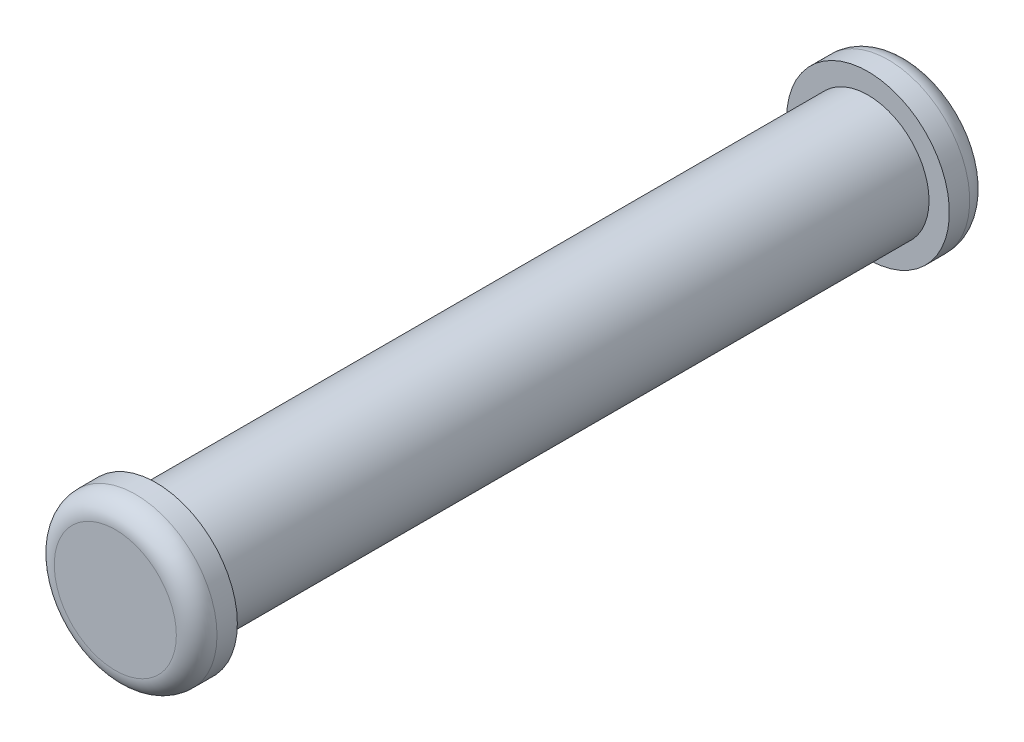
SolidWorks part; units mm, degrees
ref_plane "Front Plane" through (0, 0, 0) normal (0, 0, 1) x (1, 0, 0)
ref_plane "Top Plane" through (0, 0, 0) normal (0, 1, 0) x (1, 0, 0)
ref_plane "Right Plane" through (0, 0, 0) normal (1, 0, 0) x (0, 0, -1)
sketch "Sketch1" plane through (0, 0, 0) normal (0, 0, 1) x (1, 0, 0)
  circle A0 centre (0, 0) radius 1.5
  dimension "D1" = 3
extrude "Boss-Extrude1" add sketch "Sketch1" along normal blind 17.5
sketch "Sketch2" plane through (0, 0, 0) normal (0, 0, -1) x (-1, 0, 0)
  circle A0 centre (0, 0) radius 2
  dimension "D1" = 4
extrude "Boss-Extrude2" add sketch "Sketch2" along normal blind 1
sketch "Sketch3" plane through (0, 0, 17.5) normal (0, 0, 1) x (1, 0, 0)
  circle A1 centre (0, 0) radius 2
  circle A2 centre (0, 0) radius 2
  dimension "D1" = 0
extrude "Boss-Extrude3" add sketch "Sketch3" along normal blind 1
fillet "Fillet1" radius 0.5 2 edges at (-2, 0, -1) (2, 0, 18.5)
